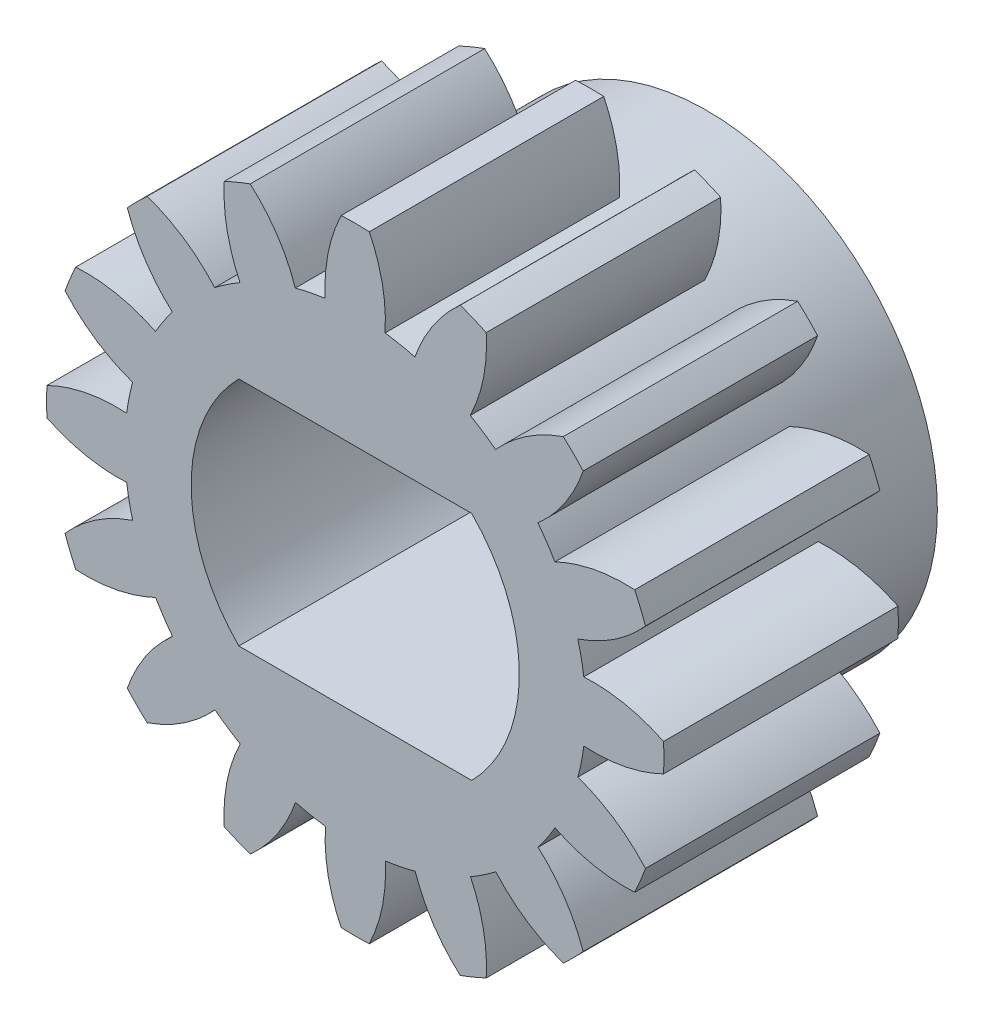
SolidWorks part; units mm, degrees
ref_plane "Front" through (0, 0, 0) normal (0, 0, 1) x (1, 0, 0)
ref_plane "Top" through (0, 0, 0) normal (0, 1, 0) x (1, 0, 0)
ref_plane "Right" through (0, 0, 0) normal (1, 0, 0) x (0, 0, -1)
sketch "草图1" plane through (0, 0, 0) normal (0, 0, 1) x (1, 0, 0)
  line L0 (-0.5753, 4.3702) -> (0, 0) construction
  line L1 (0, 0) -> (0.6752, 5.1283) construction
  line L2 (0, 4.5419) -> (0, -0.3951) construction
  arc A0 (-0.3849, 2.9248) -> (-0.7669, 2.8486) centre (0, 0) ccw
  arc A1 (0.18, 3.9459) -> (-0.18, 3.9459) centre (0, 0) ccw
  arc A3 (1.6763, 3.5767) -> (1.3437, 3.7144) centre (0, 0) ccw
  arc A4 (2.9174, 2.6629) -> (2.6629, 2.9174) centre (0, 0) ccw
  arc A5 (3.7144, 1.3438) -> (3.5767, 1.6763) centre (0, 0) ccw
  arc A6 (3.9459, -0.18) -> (3.9459, 0.18) centre (0, 0) ccw
  arc A7 (3.5767, -1.6763) -> (3.7144, -1.3437) centre (0, 0) ccw
  arc A8 (2.6629, -2.9174) -> (2.9174, -2.6629) centre (0, 0) ccw
  arc A9 (1.3438, -3.7144) -> (1.6763, -3.5767) centre (0, 0) ccw
  arc A10 (-0.18, -3.9459) -> (0.18, -3.9459) centre (0, 0) ccw
  arc A11 (-1.6763, -3.5767) -> (-1.3437, -3.7144) centre (0, 0) ccw
  arc A12 (-2.9174, -2.6629) -> (-2.6629, -2.9174) centre (0, 0) ccw
  arc A13 (-3.7144, -1.3438) -> (-3.5767, -1.6763) centre (0, 0) ccw
  arc A14 (-3.9459, 0.18) -> (-3.9459, -0.18) centre (0, 0) ccw
  arc A15 (-3.5767, 1.6763) -> (-3.7144, 1.3437) centre (0, 0) ccw
  arc A16 (-2.6629, 2.9174) -> (-2.9174, 2.6629) centre (0, 0) ccw
  arc A17 (-1.3438, 3.7144) -> (-1.6763, 3.5767) centre (0, 0) ccw
  arc A18 (0.7637, 2.8494) -> (0.3816, 2.9252) centre (0, 0) ccw
  arc A19 (1.796, 2.3403) -> (1.472, 2.5565) centre (0, 0) ccw
  arc A20 (2.5549, 1.4749) -> (2.3383, 1.7986) centre (0, 0) ccw
  arc A21 (2.9248, 0.3849) -> (2.8486, 0.7669) centre (0, 0) ccw
  arc A22 (2.8494, -0.7637) -> (2.9252, -0.3816) centre (0, 0) ccw
  arc A23 (-1.4749, 2.5549) -> (-1.7986, 2.3383) centre (0, 0) ccw
  arc A24 (-2.3403, 1.796) -> (-2.5565, 1.472) centre (0, 0) ccw
  arc A25 (-2.8494, 0.7637) -> (-2.9252, 0.3816) centre (0, 0) ccw
  arc A26 (-2.9248, -0.3849) -> (-2.8486, -0.7669) centre (0, 0) ccw
  arc A27 (-2.5549, -1.4749) -> (-2.3383, -1.7986) centre (0, 0) ccw
  arc A28 (-1.796, -2.3403) -> (-1.472, -2.5565) centre (0, 0) ccw
  arc A29 (-0.7637, -2.8494) -> (-0.3816, -2.9252) centre (0, 0) ccw
  arc A30 (0.3849, -2.9248) -> (0.7669, -2.8486) centre (0, 0) ccw
  arc A31 (1.4749, -2.5549) -> (1.7986, -2.3383) centre (0, 0) ccw
  arc A32 (2.3403, -1.796) -> (2.5565, -1.472) centre (0, 0) ccw
  spline S0 degree 2 poles (0.18, 3.9459) (0.4148, 3.4616) (0.3816, 2.9252) knots 0 0 0 1 1 1
  spline S1 degree 2 poles (-0.18, 3.9459) (-0.4124, 3.461) (-0.3849, 2.9248) knots 0 0 0 1 1 1
  spline S2 degree 2 poles (1.6763, 3.5767) (1.7079, 3.0394) (1.472, 2.5565) knots 0 0 0 1 1 1
  spline S3 degree 2 poles (1.3437, 3.7144) (0.9435, 3.3554) (0.7637, 2.8494) knots 0 0 0 1 1 1
  spline S4 degree 2 poles (2.9174, 2.6629) (2.7411, 2.1544) (2.3383, 1.7986) knots 0 0 0 1 1 1
  spline S5 degree 2 poles (2.6629, 2.9174) (2.1557, 2.7389) (1.796, 2.3403) knots 0 0 0 1 1 1
  spline S6 degree 2 poles (3.7144, 1.3438) (3.3569, 0.9415) (2.8486, 0.7669) knots 0 0 0 1 1 1
  spline S7 degree 2 poles (3.5767, 1.6763) (3.0398, 1.7055) (2.5549, 1.4749) knots 0 0 0 1 1 1
  spline S8 degree 2 poles (3.9459, -0.18) (3.4616, -0.4148) (2.9252, -0.3816) knots 0 0 0 1 1 1
  spline S9 degree 2 poles (3.9459, 0.18) (3.461, 0.4124) (2.9248, 0.3849) knots 0 0 0 1 1 1
  spline S10 degree 2 poles (3.5767, -1.6763) (3.0394, -1.7079) (2.5565, -1.472) knots 0 0 0 1 1 1
  spline S11 degree 2 poles (3.7144, -1.3437) (3.3554, -0.9435) (2.8494, -0.7637) knots 0 0 0 1 1 1
  spline S12 degree 2 poles (2.6629, -2.9174) (2.1544, -2.7411) (1.7986, -2.3383) knots 0 0 0 1 1 1
  spline S13 degree 2 poles (2.9174, -2.6629) (2.7389, -2.1557) (2.3403, -1.796) knots 0 0 0 1 1 1
  spline S14 degree 2 poles (1.3438, -3.7144) (0.9415, -3.3569) (0.7669, -2.8486) knots 0 0 0 1 1 1
  spline S15 degree 2 poles (1.6763, -3.5767) (1.7055, -3.0398) (1.4749, -2.5549) knots 0 0 0 1 1 1
  spline S16 degree 2 poles (-0.18, -3.9459) (-0.4148, -3.4616) (-0.3816, -2.9252) knots 0 0 0 1 1 1
  spline S17 degree 2 poles (0.18, -3.9459) (0.4124, -3.461) (0.3849, -2.9248) knots 0 0 0 1 1 1
  spline S18 degree 2 poles (-1.6763, -3.5767) (-1.7079, -3.0394) (-1.472, -2.5565) knots 0 0 0 1 1 1
  spline S19 degree 2 poles (-1.3437, -3.7144) (-0.9435, -3.3554) (-0.7637, -2.8494) knots 0 0 0 1 1 1
  spline S20 degree 2 poles (-2.9174, -2.6629) (-2.7411, -2.1544) (-2.3383, -1.7986) knots 0 0 0 1 1 1
  spline S21 degree 2 poles (-2.6629, -2.9174) (-2.1557, -2.7389) (-1.796, -2.3403) knots 0 0 0 1 1 1
  spline S22 degree 2 poles (-3.7144, -1.3438) (-3.3569, -0.9415) (-2.8486, -0.7669) knots 0 0 0 1 1 1
  spline S23 degree 2 poles (-3.5767, -1.6763) (-3.0398, -1.7055) (-2.5549, -1.4749) knots 0 0 0 1 1 1
  spline S24 degree 2 poles (-3.9459, 0.18) (-3.4616, 0.4148) (-2.9252, 0.3816) knots 0 0 0 1 1 1
  spline S25 degree 2 poles (-3.9459, -0.18) (-3.461, -0.4124) (-2.9248, -0.3849) knots 0 0 0 1 1 1
  spline S26 degree 2 poles (-3.5767, 1.6763) (-3.0394, 1.7079) (-2.5565, 1.472) knots 0 0 0 1 1 1
  spline S27 degree 2 poles (-3.7144, 1.3437) (-3.3554, 0.9435) (-2.8494, 0.7637) knots 0 0 0 1 1 1
  spline S28 degree 2 poles (-2.6629, 2.9174) (-2.1544, 2.7411) (-1.7986, 2.3383) knots 0 0 0 1 1 1
  spline S29 degree 2 poles (-2.9174, 2.6629) (-2.7389, 2.1557) (-2.3403, 1.796) knots 0 0 0 1 1 1
  spline S30 degree 2 poles (-1.3438, 3.7144) (-0.9415, 3.3569) (-0.7669, 2.8486) knots 0 0 0 1 1 1
  spline S31 degree 2 poles (-1.6763, 3.5767) (-1.7055, 3.0398) (-1.4749, 2.5549) knots 0 0 0 1 1 1
  point P9 (0, 3.95)
  point P10 (-0.18, 3.9459)
  point P11 (0.18, 3.9459)
  point P12 (0.35, 3.4373)
  point P13 (-0.3496, 3.4373)
  point P14 (0, 3.4551)
  point P15 (-0.3849, 2.9248)
  point P16 (0.3816, 2.9252)
  point P113 (0, 0)
  dimension "D1" = 5.9
  dimension "D2" = 7.9
  dimension "D3" = 0.18
  dimension "D4" = 0.18
  dimension "D5" = 0.35
  dimension "D6" = 0.35
  dimension "D8" = 0.7665
  dimension "D7" = 16
extrude "凸台-拉伸1" add sketch "草图1" along normal blind 4.5
sketch "草图2" plane through (0, 0, 0) normal (0, 0, -1) x (-1, 0, 0)
  circle A0 centre (0, 0) radius 2.95
  circle A1 centre (0, 0) radius 4.6296
extrude "切除-拉伸1" cut sketch "草图2" against normal blind 1.5
sketch "草图3" plane through (0, 0, 4.5) normal (0, 0, 1) x (1, 0, 0)
  line L0 (-1.4898, 1.48) -> (1.4898, 1.48)
  line L1 (-1.4898, -1.48) -> (1.4898, -1.48)
  arc A0 (-1.4898, 1.48) -> (-1.4898, -1.48) centre (0, 0) ccw
  arc A1 (1.4898, -1.48) -> (1.4898, 1.48) centre (0, 0) ccw
  dimension "D1" = 1.48
  dimension "D2" = 1.48
extrude "切除-拉伸2" cut sketch "草图3" against normal through all
